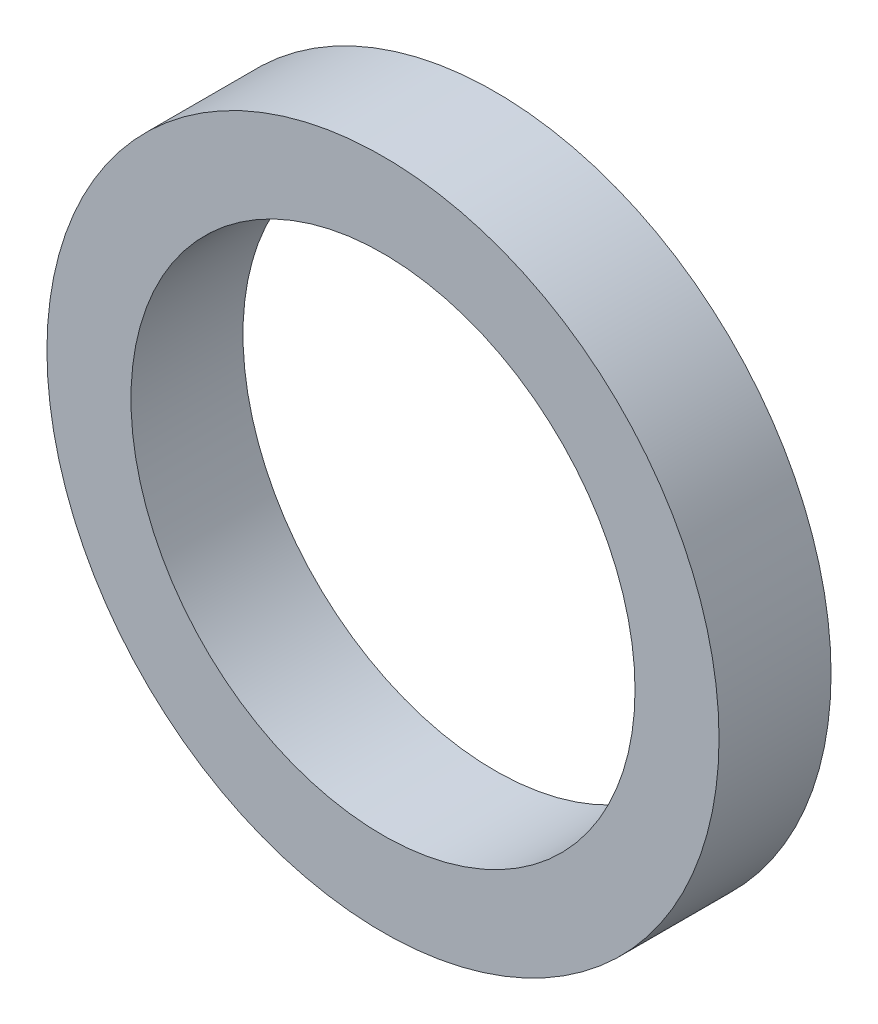
SolidWorks part; units mm, degrees
ref_plane "前视基准面" through (0, 0, 0) normal (0, 0, 1) x (1, 0, 0)
ref_plane "上视基准面" through (0, 0, 0) normal (0, 1, 0) x (1, 0, 0)
ref_plane "右视基准面" through (0, 0, 0) normal (1, 0, 0) x (0, 0, -1)
sketch "草图1" plane through (0, 0, 0) normal (0, 0, 1) x (1, 0, 0)
  circle A0 centre (0, 0) radius 3
  circle A1 centre (0, 0) radius 2.25
extrude "凸台-拉伸1" add sketch "草图1" along normal blind 1
